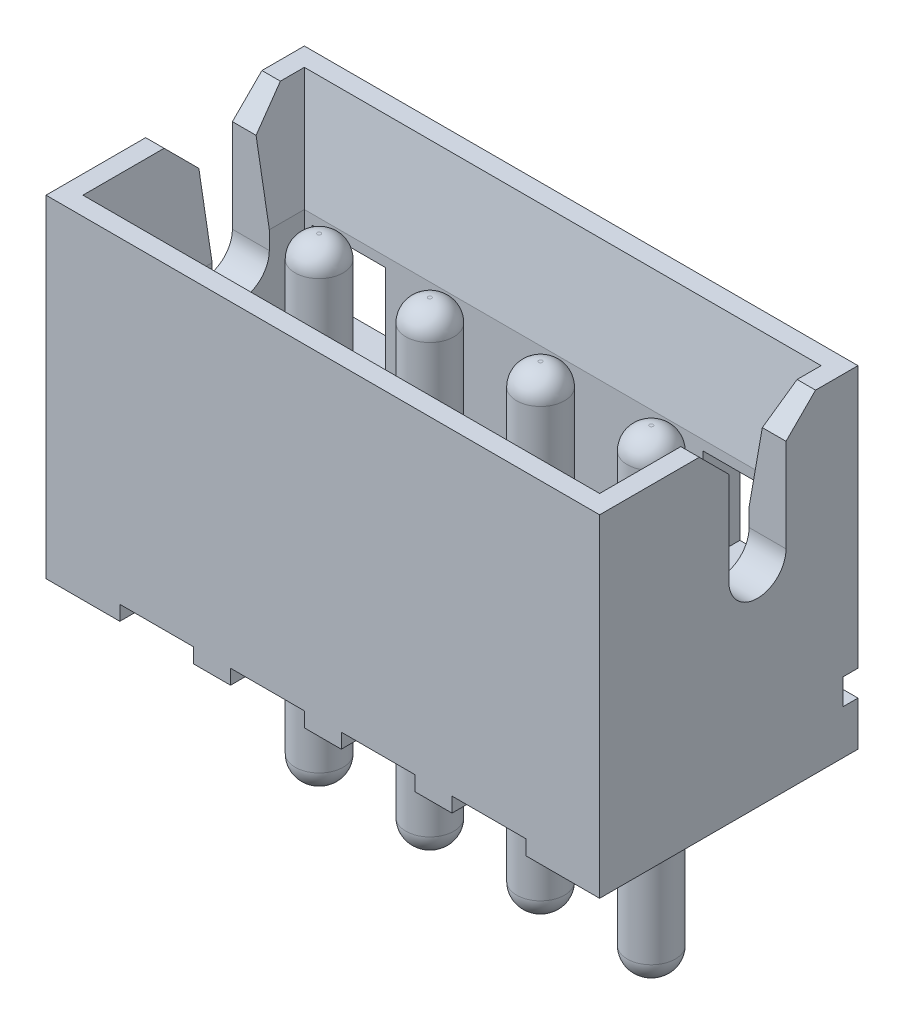
SolidWorks part; units mm, degrees
ref_plane "Спереди" through (0, 0, 0) normal (0, 0, 1) x (1, 0, 0)
ref_plane "Сверху" through (0, 0, 0) normal (0, 1, 0) x (1, 0, 0)
ref_plane "Справа" through (0, 0, 0) normal (1, 0, 0) x (0, 0, -1)
sketch "Эскиз1" plane through (0, 0, 0) normal (0, 1, 0) x (1, 0, 0)
  line L0 (-3.75, 0.45) -> (3.75, 0.45) construction
  line L1 (3.75, 1.75) -> (-3.75, 1.75)
  line L2 (3.75, 1.75) -> (3.75, -1.75)
  line L3 (3.75, -1.75) -> (-3.75, -1.75)
  line L4 (-3.75, 1.75) -> (-3.75, -1.75)
  line L5 (3.75, 1.75) -> (-3.75, -1.75) construction
  line L6 (3.75, -1.75) -> (-3.75, 1.75) construction
  circle A0 centre (-2.25, 0.45) radius 0.325
  circle A1 centre (-0.75, 0.45) radius 0.325
  circle A2 centre (0.75, 0.45) radius 0.325
  circle A3 centre (2.25, 0.45) radius 0.325
  point P0 (0, 0)
  dimension "D3" = 0.65
  dimension "D1" = 3.5
  dimension "D2" = 7.5
  dimension "D4" = 1.5
  dimension "D5" = 1.5
  dimension "D6" = 1.5
  dimension "D7" = 1.5
  dimension "D8" = 2.2
extrude "Бобышка-Вытянуть1" add sketch "Эскиз1" along normal blind 4.5 contours L1 L4 L3 L2 A3 A2 A1 A0
sketch "Эскиз2" plane through (0, 4.5, 0) normal (0, 1, 0) x (1, 0, 0)
  line L18 (3.25, -1.25) -> (3.25, 1.25)
  line L19 (-3.25, -1.25) -> (3.25, -1.25)
  line L20 (3.25, 1.25) -> (-3.25, 1.25)
  line L21 (-3.25, 1.25) -> (-3.25, -1.25)
  line L22 (3.25, -1.25) -> (3.25, 1.25)
  line L23 (-3.25, -1.25) -> (3.25, -1.25)
  line L24 (3.25, 1.25) -> (-3.25, 1.25)
  line L25 (-3.25, 1.25) -> (-3.25, -1.25)
  dimension "D1" = 0.5
extrude "Вырез-Вытянуть1" cut sketch "Эскиз2" against normal blind 4
sketch "Эскиз3" plane through (0, 4.5, 0) normal (0, 1, 0) x (1, 0, 0)
  line L8 (3.5, 1.5) -> (-3.5, 1.5)
  line L9 (-3.5, 1.5) -> (-3.5, -1.5)
  line L10 (-3.5, -1.5) -> (3.5, -1.5)
  line L11 (3.5, -1.5) -> (3.5, 1.5)
  line L12 (3.5, 1.5) -> (-3.5, 1.5)
  line L13 (-3.5, 1.5) -> (-3.5, -1.5)
  line L14 (-3.5, -1.5) -> (3.5, -1.5)
  line L15 (3.5, -1.5) -> (3.5, 1.5)
  dimension "D1" = 0.25
extrude "Вырез-Вытянуть2" cut sketch "Эскиз3" against normal blind 2 draft 10
sketch "Эскиз4" plane through (0, 0, -1.75) normal (0, 0, -1) x (-1, 0, 0)
  line L0 (-3.75, 0.6) -> (3.75, 0.6)
  line L1 (-3.75, 4.5) -> (-3.75, 0) construction
  line L2 (3.75, 4.5) -> (3.75, 0) construction
  line L3 (-3.75, 0.95) -> (3.75, 0.95)
  line L4 (-3.75, 0.6) -> (-3.75, 0.95)
  line L5 (3.75, 0.6) -> (3.75, 0.95)
  line L6 (-3.75, 0) -> (3.75, 0) construction
  dimension "D1" = 0.35
  dimension "D2" = 0.6
extrude "Вырез-Вытянуть3" cut sketch "Эскиз4" against normal blind 0.2
sketch "Эскиз5" plane through (0, 0, 0) normal (0, -1, 0) x (1, 0, 0)
  line L0 (2.25, 1.75) -> (2.25, -1.75) construction
  line L1 (3.75, -1.75) -> (-3.75, -1.75) construction
  line L3 (3.75, 1.75) -> (-3.75, 1.75) construction
  line L4 (2.75, -1.75) -> (2.75, 1.75)
  line L5 (1.75, -1.75) -> (1.75, 1.75)
  line L6 (2.75, -1.75) -> (1.75, -1.75)
  line L7 (2.75, 1.75) -> (1.75, 1.75)
  point P11 (2.25, -0.45)
  dimension "D1" = 1
extrude "Вырез-Вытянуть4" cut sketch "Эскиз5" against normal blind 0.2
pattern_linear "Линейный массив2" count 4 spacing 1.5 along (-1, 0, 0) of "Вырез-Вытянуть4"
sketch "Эскиз6" plane through (0, 0, -1.75) normal (0, 0, -1) x (-1, 0, 0)
  line L0 (-3.75, 4.5) -> (-3.75, 0.95) construction
  line L1 (-3.15, 2.95) -> (-2.15, 2.95)
  line L2 (-3.15, 2.95) -> (-3.15, 1.65)
  line L3 (-3.15, 1.65) -> (-2.15, 1.65)
  line L4 (-2.15, 2.95) -> (-2.15, 1.65)
  line L5 (3.75, 0.95) -> (-3.75, 0.95) construction
  dimension "D1" = 1
  dimension "D2" = 1.3
  dimension "D3" = 0.6
  dimension "D4" = 0.7
extrude "Вырез-Вытянуть5" cut sketch "Эскиз6" against normal up to next (0.5 mm away)
mirror "Зеркальное отражение1" about plane through (0, 0, 0) normal (1, 0, 0) of "Вырез-Вытянуть5"
sketch "Эскиз7" plane through (-3.75, 0, 0) normal (-1, 0, 0) x (0, 0, 1)
  line L0 (0, 4.5) -> (0, 2.8379)
  line L1 (-1.75, 4.5) -> (1.75, 4.5) construction
  line L2 (-0.775, 4.5) -> (0, 4.5)
  line L3 (-0.775, 2.8379) -> (-0.775, 4.5)
  arc A0 (-0.775, 2.8379) -> (0, 2.8379) centre (-0.3875, 2.8379) ccw
  dimension "D1" = 1.6621
extrude "Вырез-Вытянуть6" cut sketch "Эскиз7" against normal through all
chamfer "Фаска1" distance 0.4 angle 45 4 edges at (3.625, 4.5, 0) (3.625, 4.5, -0.775) (-3.625, 4.5, 0) (-3.625, 4.5, -0.775)
sketch "Эскиз8" plane through (0, 0, 0) normal (0, -1, 0) x (1, 0, 0)
  circle A0 centre (2.25, -0.45) radius 0.325
  circle A1 centre (2.25, -0.45) radius 0.325 construction
extrude "Бобышка-Вытянуть2" add sketch "Эскиз8" along normal blind 2.7 and the other way blind 3.7
fillet "Скругление1" radius 0.3 2 edges at (2.25, 3.7, -0.775) (2.25, -2.7, -0.775)
pattern_linear "Линейный массив3" count 4 spacing 1.5 along (-1, 0, 0) of "Бобышка-Вытянуть2", "Скругление1"
